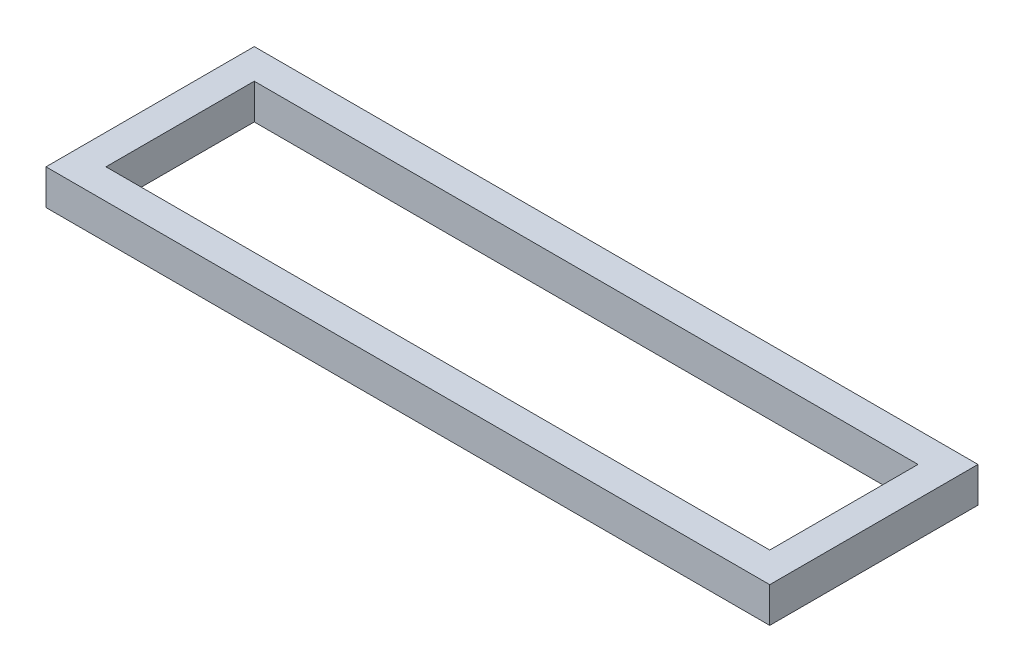
SolidWorks part; units mm, degrees
ref_plane "Alzado" through (0, 0, 0) normal (0, 0, 1) x (1, 0, 0)
ref_plane "Planta" through (0, 0, 0) normal (0, 1, 0) x (1, 0, 0)
ref_plane "Vista lateral" through (0, 0, 0) normal (1, 0, 0) x (0, 0, -1)
sketch "Croquis1" plane through (0, 0, 0) normal (0, 1, 0) x (1, 0, 0)
  line L0 (-488.125, -140.4625) -> (-488.125, 140.4625)
  line L1 (-492.125, -144.4625) -> (492.125, -144.4625)
  line L2 (-492.125, -144.4625) -> (-492.125, 144.4625) construction
  line L3 (-492.125, 144.4625) -> (492.125, 144.4625)
  line L4 (492.125, -144.4625) -> (492.125, 144.4625)
  line L5 (-492.125, -144.4625) -> (492.125, 144.4625) construction
  line L6 (-492.125, 144.4625) -> (492.125, -144.4625) construction
  line L7 (-447.675, -100.0125) -> (447.675, -100.0125)
  line L8 (-447.675, -100.0125) -> (-447.675, 100.0125)
  line L9 (-447.675, 100.0125) -> (447.675, 100.0125)
  line L10 (447.675, -100.0125) -> (447.675, 100.0125)
  line L11 (-447.675, -100.0125) -> (447.675, 100.0125) construction
  line L12 (-447.675, 100.0125) -> (447.675, -100.0125) construction
  line L13 (-488.125, 140.4625) -> (488.125, 140.4625)
  line L14 (488.125, -140.4625) -> (488.125, 140.4625)
  line L15 (-488.125, -140.4625) -> (488.125, -140.4625)
  point P0 (0, 0)
  point P6 (0, 0)
  dimension "D1" = 895.35
  dimension "D2" = 200.025
  dimension "D3" = 44.45
  dimension "D4" = 44.45
  dimension "D5" = 4
extrude "Saliente-Extruir1" add sketch "Croquis1" along normal blind 47.625 contours L0 L15 L14 L13 L10 L7 L8 L9
